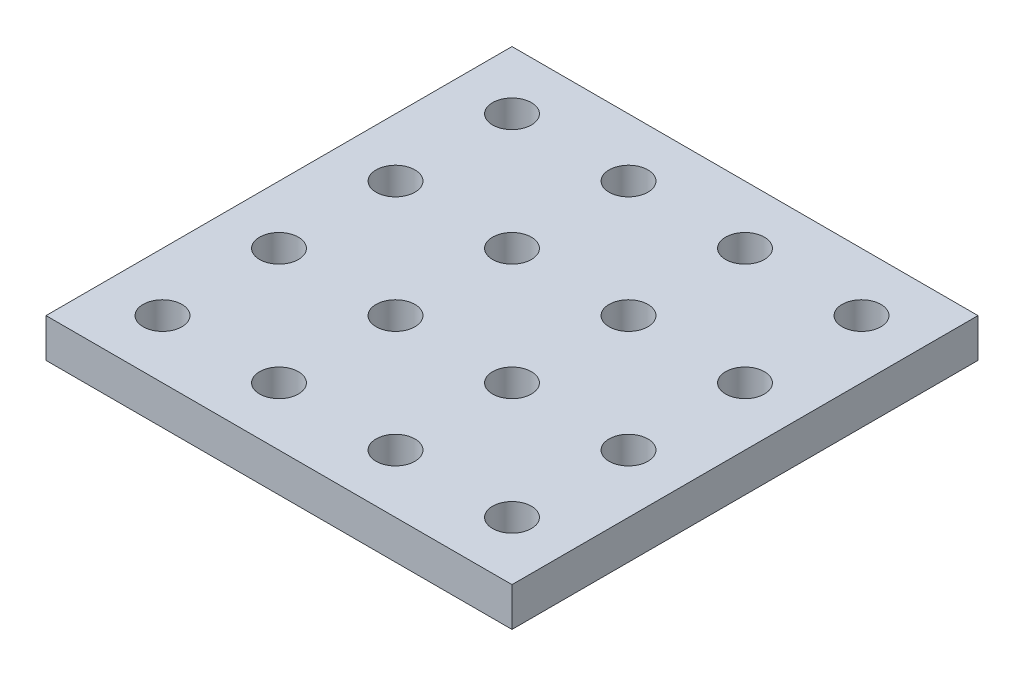
SolidWorks part; units mm, degrees
ref_plane "Front Plane" through (0, 0, 0) normal (0, 0, 1) x (1, 0, 0)
ref_plane "Top Plane" through (0, 0, 0) normal (0, 1, 0) x (1, 0, 0)
ref_plane "Right Plane" through (0, 0, 0) normal (1, 0, 0) x (0, 0, -1)
sketch "Sketch1" plane through (0, 0, 0) normal (0, 1, 0) x (1, 0, 0)
  line L1 (0, 0) -> (120, 0)
  line L2 (0, 0) -> (0, 120)
  line L3 (0, 120) -> (120, 120)
  line L4 (120, 0) -> (120, 120)
  dimension "D1" = 120
  dimension "D2" = 120
extrude "Boss-Extrude1" add sketch "Sketch1" along normal blind 10
sketch "Sketch2" plane through (0, 10, 0) normal (0, 1, 0) x (1, 0, 0)
  line L0 (0, 0) -> (120, 0) construction
  line L1 (0, 120) -> (0, 0) construction
  circle A0 centre (15, 15) radius 5
  dimension "D1" = 15
  dimension "D2" = 15
  dimension "D3" = 10
extrude "Cut-Extrude1" cut sketch "Sketch2" against normal through all
pattern_linear "LPattern1" count 4 spacing 30 along (1, 0, 0) count 4 spacing 30 along (0, 0, -1) of "Cut-Extrude1"
